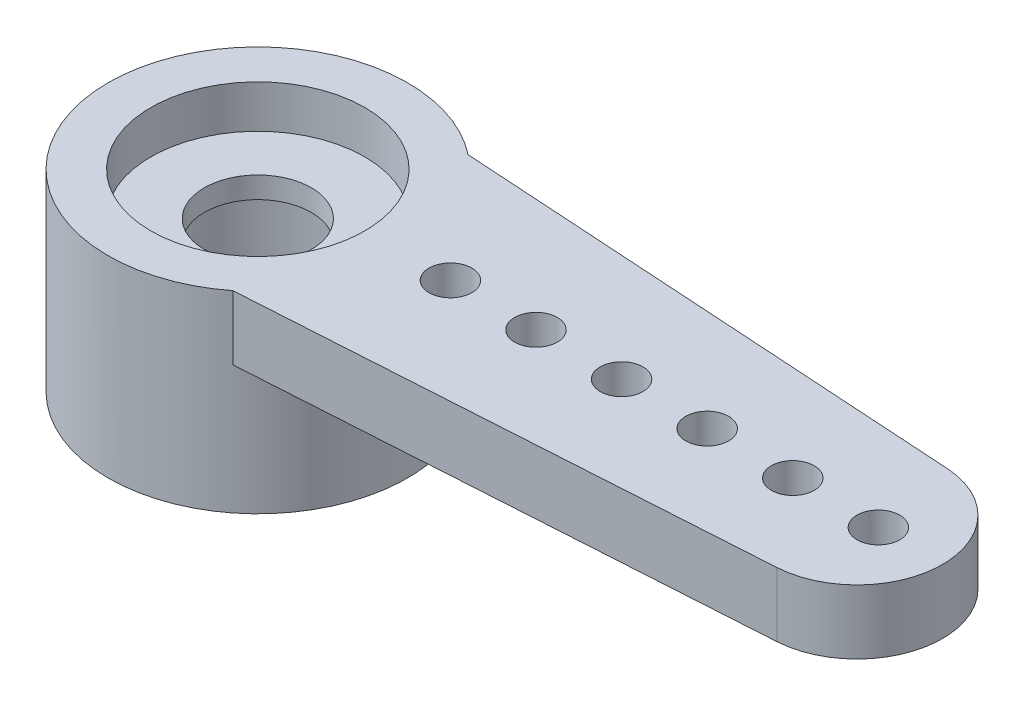
SolidWorks part; units mm, degrees
ref_plane "Front Plane" through (0, 0, 0) normal (0, 0, 1) x (1, 0, 0)
ref_plane "Top Plane" through (0, 0, 0) normal (0, 1, 0) x (1, 0, 0)
ref_plane "Right Plane" through (0, 0, 0) normal (1, 0, 0) x (0, 0, -1)
sketch "Sketch1" plane through (0, 0, 0) normal (0, 1, 0) x (1, 0, 0)
  circle A0 centre (0, 0) radius 3.5
  dimension "D1" = 7
extrude "Boss-Extrude1" add sketch "Sketch1" along normal blind 4.5
sketch "Sketch2" plane through (0, 4.5, 0) normal (0, 1, 0) x (1, 0, 0)
  circle A0 centre (0, 0) radius 2.5
  dimension "D1" = 5
extrude "Cut-Extrude1" cut sketch "Sketch2" against normal blind 1
sketch "Sketch3" plane through (0, 0, 0) normal (0, -1, 0) x (1, 0, 0)
  circle A0 centre (0, 0) radius 2.5
  dimension "D1" = 5
extrude "Cut-Extrude2" cut sketch "Sketch3" against normal blind 3
sketch "Sketch4" plane through (0, 3.5, 0) normal (0, 1, 0) x (1, 0, 0)
  circle A0 centre (0, 0) radius 1.25
  dimension "D1" = 2.5
extrude "Cut-Extrude3" cut sketch "Sketch4" against normal through all
sketch "Sketch5" plane through (0, 4.5, 0) normal (0, 1, 0) x (1, 0, 0)
  line L0 (2.1651, 2.75) -> (14.1258, 1.996)
  line L1 (2.1651, -2.75) -> (14.1258, -1.996)
  circle A0 centre (0, 0) radius 3.5 construction
  arc A1 (2.1651, -2.75) -> (2.1651, 2.75) centre (0, 0) ccw
  arc A2 (14.1258, -1.996) -> (14.1258, 1.996) centre (14, 0) ccw
  dimension "D1" = 19.5
  dimension "D3" = 2
  dimension "D2" = 5.5
extrude "Boss-Extrude2" add sketch "Sketch5" against normal blind 1.5
sketch "Sketch6" plane through (0, 4.5, 0) normal (0, 1, 0) x (1, 0, 0)
  line L0 (4.5, 0) -> (6.5, 0) construction
  line L1 (6.5, 0) -> (8.5, 0) construction
  line L2 (8.5, 0) -> (10.5, 0) construction
  line L3 (10.5, 0) -> (12.5, 0) construction
  line L4 (12.5, 0) -> (14.5, 0) construction
  line L5 (0, 0) -> (4.5, 0) construction
  arc A1 (14.1258, -1.996) -> (14.1258, 1.996) centre (14, 0) ccw construction
  circle A2 centre (4.5, 0) radius 0.5
  circle A3 centre (6.5, 0) radius 0.5
  circle A4 centre (8.5, 0) radius 0.5
  circle A5 centre (10.5, 0) radius 0.5
  circle A6 centre (12.5, 0) radius 0.5
  circle A7 centre (14.5, 0) radius 0.5
  dimension "D3" = 1
  dimension "D1" = 10
  dimension "D2" = 1.5
extrude "Cut-Extrude4" cut sketch "Sketch6" against normal through all
